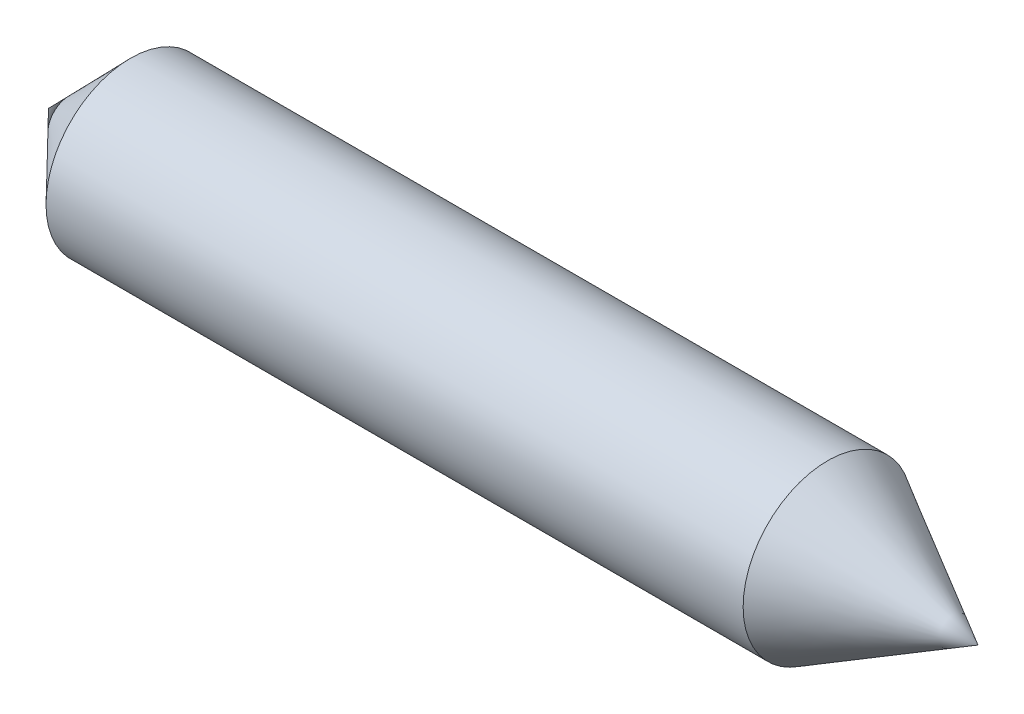
SolidWorks part; units mm, degrees
ref_plane "Alzado" through (0, 0, 0) normal (0, 0, 1) x (1, 0, 0)
ref_plane "Planta" through (0, 0, 0) normal (0, 1, 0) x (1, 0, 0)
ref_plane "Vista lateral" through (0, 0, 0) normal (1, 0, 0) x (0, 0, -1)
sketch "Croquis1" plane through (0, 0, 0) normal (0, 0, 1) x (1, 0, 0)
  line L0 (-79.0532, 7.1848) -> (120.9468, 7.1848)
  line L1 (120.9468, 7.1848) -> (88.5907, 25.3633)
  line L2 (88.5907, 25.3633) -> (-61.4093, 25.3633)
  line L3 (-61.4093, 25.3633) -> (-79.0532, 7.1848)
  dimension "D1" = 150
  dimension "D2" = 200
revolve "Revolución2" add sketch "Croquis1" angle 360 about L0
